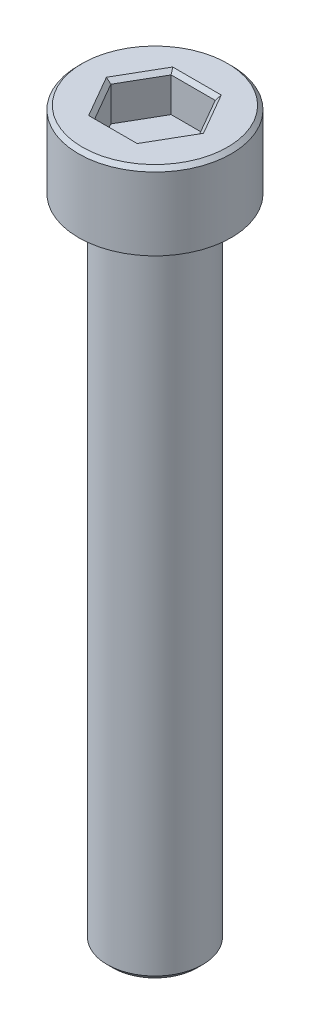
SolidWorks part; units mm, degrees
ref_plane "前视基准面" through (0, 0, 0) normal (0, 0, 1) x (1, 0, 0)
ref_plane "上视基准面" through (0, 0, 0) normal (0, 1, 0) x (1, 0, 0)
ref_plane "右视基准面" through (0, 0, 0) normal (1, 0, 0) x (0, 0, -1)
sketch "草图1" plane through (0, 0, 0) normal (0, 1, 0) x (1, 0, 0)
  circle A0 centre (0, 0) radius 4
  dimension "D1" = 8
extrude "凸台-拉伸1" add sketch "草图1" along normal blind 4
sketch "草图2" plane through (0, 0, 0) normal (0, -1, 0) x (1, 0, 0)
  circle A0 centre (0, 0) radius 2.5
  dimension "D1" = 5
extrude "凸台-拉伸2" add sketch "草图2" along normal blind 34
sketch "草图11" plane through (0, 4, 0) normal (0, 1, 0) x (1, 0, 0)
  line L1 (1.155, 1.9999) -> (-1.1544, 2.0001)
  line L2 (-1.1544, 2.0001) -> (-2.3094, 0.0003)
  line L3 (-2.3094, 0.0003) -> (-1.155, -1.9999)
  line L4 (-1.155, -1.9999) -> (1.1544, -2.0001)
  line L5 (1.1544, -2.0001) -> (2.3094, -0.0003)
  line L6 (2.3094, -0.0003) -> (1.155, 1.9999)
  circle A0 centre (0, 0) radius 2 construction
  dimension "D1" = 4
extrude "切除-拉伸1" cut sketch "草图11" against normal blind 2
chamfer "倒角1" distance 0.2 angle 45 7 edges at (0, 4, 4) (0.0003, 4, -2) (-1.7319, 4, -1.0002) (-1.7322, 4, 0.9998) (-0.0003, 4, 2) (1.7319, 4, 1.0002) (1.7322, 4, -0.9998)
chamfer "倒角2" distance 0.3 angle 45 1 edges at (0, -34, -2.5)
